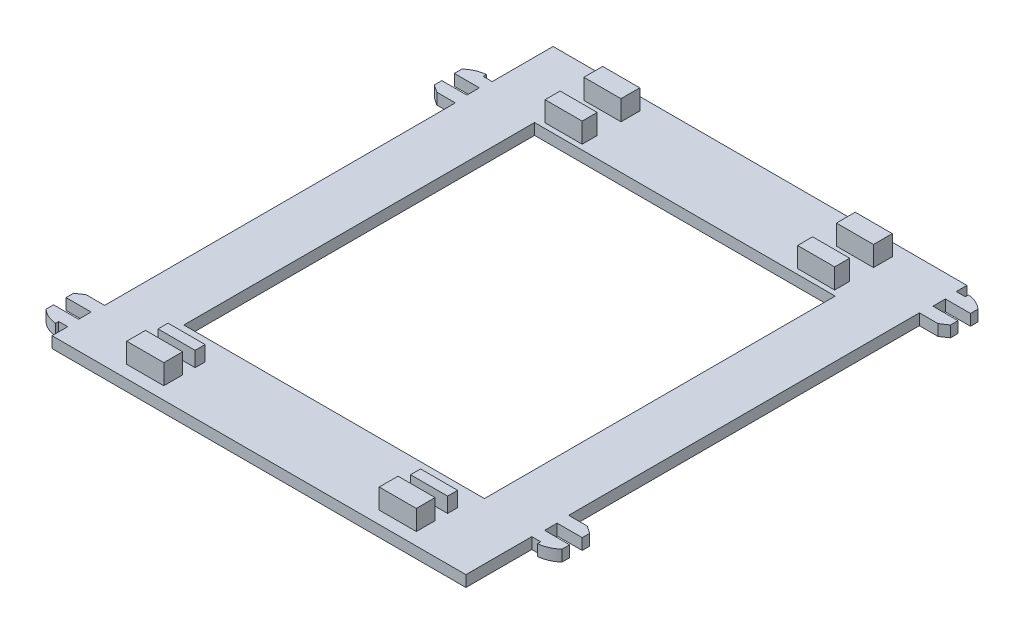
SolidWorks part; units mm, degrees
ref_plane "Front" through (0, 0, 0) normal (0, 0, 1) x (1, 0, 0)
ref_plane "Top" through (0, 0, 0) normal (0, 1, 0) x (1, 0, 0)
ref_plane "Right" through (0, 0, 0) normal (1, 0, 0) x (0, 0, -1)
sketch "Sketch1" plane through (0, 0, 0) normal (0, 1, 0) x (1, 0, 0)
  line L0 (43.1, 45.51) -> (46.5, 45.51)
  line L1 (-41.3, 50) -> (41.3, 50)
  line L2 (-41.3, 50) -> (-41.3, -50)
  line L3 (-41.3, -50) -> (41.3, -50)
  line L4 (41.3, 50) -> (41.3, -50)
  line L5 (-41.3, 50) -> (41.3, -50) construction
  line L6 (-41.3, -50) -> (41.3, 50) construction
  line L7 (41.3, 47.87) -> (43.1, 47.87)
  line L8 (41.3, 47.87) -> (41.3, 45.51)
  line L9 (41.3, 45.51) -> (43.1, 45.51)
  line L10 (43.1, 47.87) -> (43.1, 45.51)
  line L11 (46.5, 45.51) -> (46.5, 47.01)
  line L12 (43.1, 47.87) -> (43.1, 48.52)
  line L13 (41.3, 45.51) -> (41.5, 45.51)
  line L14 (41.3, 45.51) -> (41.3, 43.01)
  line L15 (41.3, 43.01) -> (41.5, 43.01)
  line L16 (41.5, 45.51) -> (41.5, 43.01)
  line L17 (41.5, 43.01) -> (46.5, 43.01)
  line L18 (46.5, 43.01) -> (46.5, 41.51)
  line L19 (46.5, 41.51) -> (45, 40.51)
  line L20 (45, 40.51) -> (41.3, 40.51)
  line L21 (41.3, 5.51) -> (60.4529, 5.51) construction
  line L22 (41.5, -31.99) -> (46.5, -31.99)
  line L23 (46.5, -31.99) -> (46.5, -30.49)
  line L24 (46.5, -30.49) -> (45, -29.49)
  line L25 (45, -29.49) -> (41.3, -29.49)
  line L26 (43.1, -36.85) -> (43.1, -37.5)
  line L27 (46.5, -34.49) -> (46.5, -35.99)
  line L28 (43.1, -34.49) -> (46.5, -34.49)
  line L29 (41.3, -34.49) -> (43.1, -34.49)
  line L30 (43.1, -36.85) -> (43.1, -34.49)
  line L31 (41.3, -36.85) -> (43.1, -36.85)
  line L32 (41.3, -36.85) -> (41.3, -34.49)
  line L33 (41.3, -31.99) -> (41.5, -31.99)
  line L34 (41.5, -34.49) -> (41.5, -31.99)
  line L35 (41.3, -34.49) -> (41.5, -34.49)
  line L36 (41.3, -34.49) -> (41.3, -31.99)
  line L37 (0, 36.7793) -> (0, -23.6766) construction
  line L38 (-41.3, -4.51) -> (-64.7336, -4.51) construction
  line L39 (-45, -39.51) -> (-41.3, -39.51)
  line L40 (-46.5, -40.51) -> (-45, -39.51)
  line L41 (-46.5, -42.01) -> (-46.5, -40.51)
  line L42 (-41.5, -42.01) -> (-46.5, -42.01)
  line L43 (-41.5, -44.51) -> (-41.5, -42.01)
  line L44 (-41.3, -44.51) -> (-46.5, -44.51)
  line L45 (-43.1, -46.87) -> (-41.3, -46.87)
  line L46 (-43.1, -46.87) -> (-43.1, -47.52)
  line L47 (-46.5, -44.51) -> (-46.5, -46.01)
  line L59 (-41.3, 47.87) -> (-41.3, 45.51)
  line L60 (-41.3, 47.87) -> (-41.3, 37.87) construction
  line L61 (-43.1, 37.85) -> (-41.3, 37.85)
  line L62 (-43.1, 37.85) -> (-43.1, 38.5)
  line L63 (-41.3, 35.49) -> (-46.5, 35.49)
  line L64 (-46.5, 35.49) -> (-46.5, 36.99)
  line L65 (-41.5, 35.49) -> (-41.5, 32.99)
  line L66 (-41.5, 32.99) -> (-46.5, 32.99)
  line L67 (-46.5, 32.99) -> (-46.5, 31.49)
  line L68 (-46.5, 31.49) -> (-45, 30.49)
  line L69 (-45, 30.49) -> (-41.3, 30.49)
  arc A0 (43.1, 48.52) -> (46.5, 47.01) centre (42.5287, 42.6507) cw
  arc A1 (43.1, -37.5) -> (46.5, -35.99) centre (42.5287, -31.6307) ccw
  arc A2 (-46.5, -46.01) -> (-43.1, -47.52) centre (-42.5287, -41.6507) ccw
  arc A4 (-46.5, 36.99) -> (-43.1, 38.5) centre (-42.5287, 32.6307) cw
  point P0 (0, 0)
  dimension "D9" = 0.65
  dimension "D10" = 5.897
  dimension "D25" = 5.897
  dimension "D1" = 82.6
  dimension "D2" = 100
  dimension "D3" = 2.13
  dimension "D4" = 2.36
  dimension "D5" = 1.8
  dimension "D6" = 0.2
  dimension "D7" = 5.2
  dimension "D8" = 1.5
  dimension "D11" = 2.5
  dimension "D12" = 1.5
  dimension "D13" = 3.7
  dimension "D14" = 2.5
  dimension "D15" = 5.2
  dimension "D16" = 35
  dimension "D17" = 10
  dimension "D18" = 5.2
  dimension "D19" = 1.8
  dimension "D20" = 1.5
  dimension "D21" = 12.15
  dimension "D22" = 2.36
  dimension "D23" = 0.2
  dimension "D24" = 0.65
  dimension "D26" = 1.5
  dimension "D27" = 2.5
  dimension "D28" = 3.7
  dimension "D29" = 5
  dimension "D30" = 2.5
  dimension "D31" = 35
  dimension "D32" = 3.13
extrude "Boss-Extrude1" add sketch "Sketch1" along normal blind 2.23 contours L26 A1 L27 L28 L30 | L4 L31 L30 L29 | L4 L33 L22 L23 L24 L25 | L29 L34 L33 L4 | L4 L1 L2 L3 | L20 L19 L18 L17 L15 L4 | L16 L9 L4 L15 | L10 L7 L4 L9 | A0 L12 L10 L0 L11 | L47 A2 L46 L45 L2 L44 | L44 L2 L39 L40 L41 L42 L43 | L68 L69 L2 L63 L65 L66 L67 | A4 L64 L63 L2 L61 L62
sketch "Sketch2" plane through (0, 2.23, 0) normal (0, 1, 0) x (1, 0, 0)
  line L0 (-41.3, -50) -> (41.3, -50) construction
  line L1 (-21.5, -43.75) -> (-28.9, -43.75)
  line L2 (-21.5, -43.75) -> (-21.5, -47.5)
  line L3 (-21.5, -47.5) -> (-28.9, -47.5)
  line L4 (-28.9, -43.75) -> (-28.9, -47.5)
  line L5 (-41.5, -44.51) -> (-41.5, -42.01) construction
  line L6 (0, -50) -> (0, -10.7982) construction
  line L7 (21.5, -43.75) -> (21.5, -47.5)
  line L8 (21.5, -47.5) -> (28.9, -47.5)
  line L9 (28.9, -43.75) -> (28.9, -47.5)
  line L10 (21.5, -43.75) -> (28.9, -43.75)
  line L11 (-26.6786, 0) -> (25.6107, 0) construction
  line L12 (21.5, 47.5) -> (28.9, 47.5)
  line L13 (28.9, 43.75) -> (28.9, 47.5)
  line L14 (21.5, 43.75) -> (28.9, 43.75)
  line L15 (21.5, 43.75) -> (21.5, 47.5)
  line L16 (-21.5, 43.75) -> (-21.5, 47.5)
  line L17 (-21.5, 47.5) -> (-28.9, 47.5)
  line L18 (-28.9, 43.75) -> (-28.9, 47.5)
  line L19 (-21.5, 43.75) -> (-28.9, 43.75)
  line L20 (-28.9, 36) -> (-28.9, 39)
  line L21 (-28.9, -36) -> (-21.5, -36)
  line L22 (-28.9, -36) -> (-28.9, -39)
  line L23 (-28.9, -39) -> (-21.5, -39)
  line L24 (-21.5, -36) -> (-21.5, -39)
  line L25 (-28.9, 36) -> (-21.5, 36)
  line L26 (-21.5, 36) -> (-21.5, 39)
  line L27 (-28.9, 39) -> (-21.5, 39)
  line L28 (28.9, 36) -> (28.9, 39)
  line L29 (28.9, 36) -> (21.5, 36)
  line L30 (21.5, 36) -> (21.5, 39)
  line L31 (28.9, 39) -> (21.5, 39)
  line L32 (21.5, -36) -> (21.5, -39)
  line L33 (28.9, -36) -> (21.5, -36)
  line L34 (28.9, -36) -> (28.9, -39)
  line L35 (28.9, -39) -> (21.5, -39)
  dimension "D1" = 2.5
  dimension "D2" = 12.6
  dimension "D3" = 7.4
  dimension "D4" = 3.75
  dimension "D5" = 4.75
  dimension "D6" = 3
  dimension "D7" = 7.4
extrude "Boss-Extrude2" add sketch "Sketch2" along normal blind 4 contours L2 L1 L4 L3 | L7 L8 L9 L10 | L28 L31 L30 L29 | L20 L27 L26 L25 | L16 L17 L18 L19 | L12 L13 L14 L15
sketch "Sketch3" plane through (0, 2.23, 0) normal (0, 1, 0) x (1, 0, 0)
  line L1 (-30, 35) -> (30, 35)
  line L2 (-30, 35) -> (-30, -35)
  line L3 (-30, -35) -> (30, -35)
  line L4 (30, 35) -> (30, -35)
  line L5 (-30, 35) -> (30, -35) construction
  line L6 (-30, -35) -> (30, 35) construction
  point P0 (0, 0)
  dimension "D1" = 70
  dimension "D2" = 60
extrude "Cut-Extrude1" cut sketch "Sketch3" against normal blind 10
sketch "Sketch4" plane through (0, 0, 0) normal (0, -1, 0) x (1, 0, 0)
  line L0 (41.3, -40) -> (-41.3, -40) construction
  line L1 (41.3, -40.51) -> (41.3, 29.49) construction
  line L2 (-41.3, -30.49) -> (-41.3, 39.51) construction
  line L3 (-41.3, -50) -> (41.3, -50) construction
  text T0 "+Z↑"
  dimension "D1" = 10
extrude "Cut-Extrude2" cut sketch "Sketch4" against normal blind 0.5
sketch "Sketch5" plane through (0, 2.23, 0) normal (0, 1, 0) x (1, 0, 0)
  line L0 (-28.9, -43.75) -> (-28.9, -47.5) construction
  line L1 (-28.9, -41.25) -> (-21.5, -41.25)
  line L2 (-28.9, -41.25) -> (-28.9, -39.25)
  line L3 (-28.9, -39.25) -> (-21.5, -39.25)
  line L4 (-21.5, -41.25) -> (-21.5, -39.25)
  line L5 (21.5, -39.25) -> (28.9, -39.25)
  line L6 (21.5, -39.25) -> (21.5, -41.25)
  line L7 (21.5, -41.25) -> (28.9, -41.25)
  line L8 (28.9, -39.25) -> (28.9, -41.25)
  line L9 (-21.5, -43.75) -> (-21.5, -47.5) construction
  line L10 (28.9, -43.75) -> (28.9, -47.5) construction
  line L11 (21.5, -43.75) -> (21.5, -47.5) construction
  line L12 (-21.5, -39.25) -> (21.5, -39.25) construction
  line L13 (-21.5, -43.75) -> (-28.9, -43.75) construction
  line L14 (-21.5, -41.25) -> (21.5, -41.25) construction
  dimension "D1" = 2
  dimension "D2" = 2.5
extrude "Boss-Extrude3" add sketch "Sketch5" along normal blind 3
